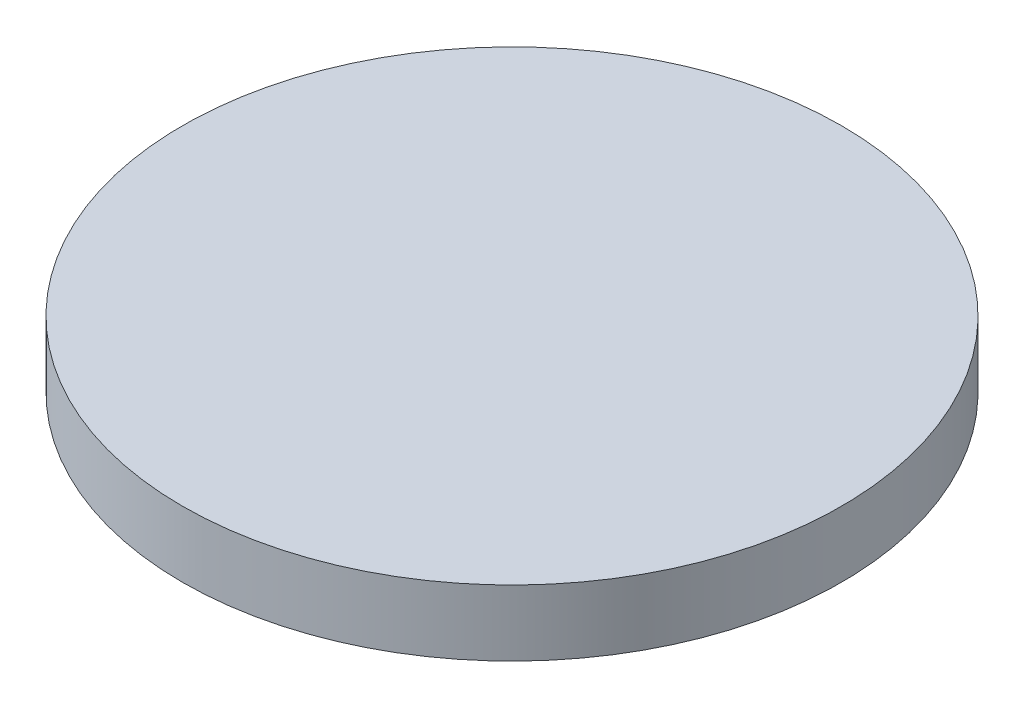
SolidWorks part; units mm, degrees
ref_plane "Plan de face" through (0, 0, 0) normal (0, 0, 1) x (1, 0, 0)
ref_plane "Plan de dessus" through (0, 0, 0) normal (0, 1, 0) x (1, 0, 0)
ref_plane "Plan de droite" through (0, 0, 0) normal (1, 0, 0) x (0, 0, -1)
sketch "Esquisse1" plane through (0, 0, 0) normal (0, 1, 0) x (1, 0, 0)
  circle A0 centre (0, 0) radius 15
  dimension "D1" = 30
extrude "Boss.-Extru.1" add sketch "Esquisse1" along normal blind 3
